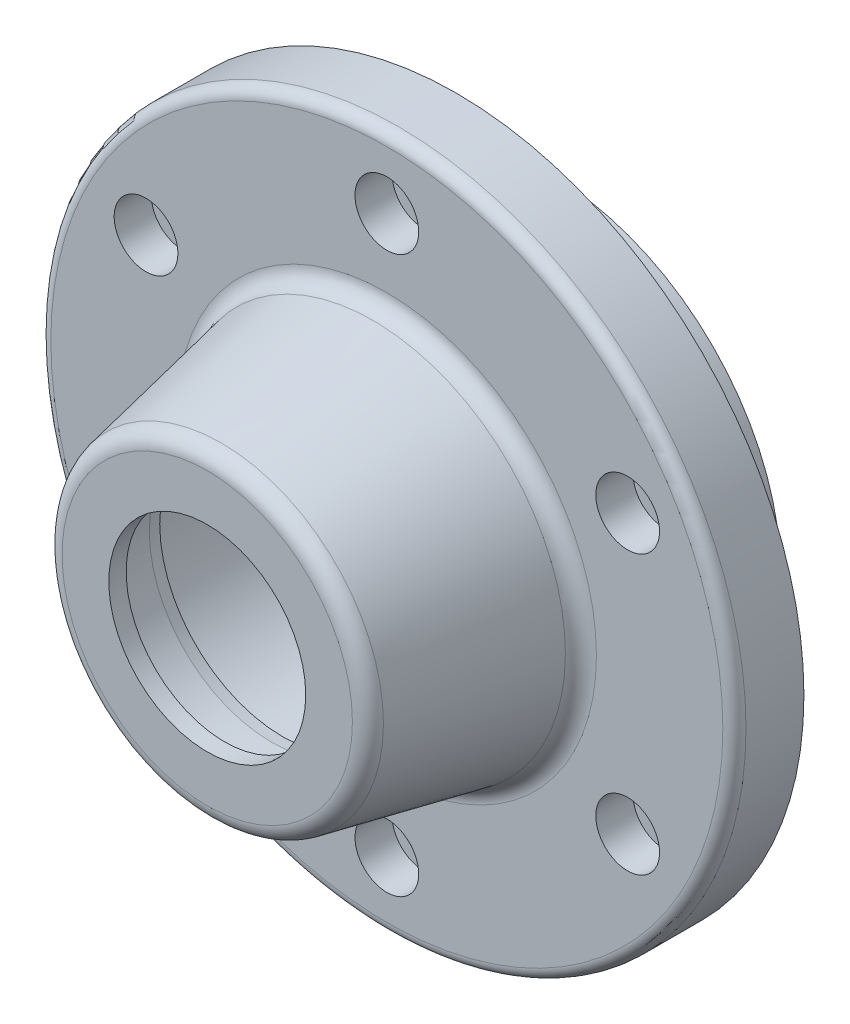
SolidWorks part; units mm, degrees
ref_plane "Front Plane" through (0, 0, 0) normal (0, 0, 1) x (1, 0, 0)
ref_plane "Top Plane" through (0, 0, 0) normal (0, 1, 0) x (1, 0, 0)
ref_plane "Right Plane" through (0, 0, 0) normal (1, 0, 0) x (0, 0, -1)
sketch "Sketch1" plane through (0, 0, 0) normal (1, 0, 0) x (0, 0, -1)
  line L0 (-82.7476, 0) -> (82.7476, 0) construction
  line L1 (55, 0) -> (-55, 0) construction
  line L2 (-63, -17) -> (-63, -25.0583)
  line L3 (-60.5883, -28) -> (-34.4117, -33.2353)
  line L4 (-32, -36.1771) -> (-32, -58)
  line L5 (-30, -60) -> (-20, -60)
  line L6 (-20, -60) -> (-20, -40)
  line L7 (-20, -40) -> (-4, -40)
  line L8 (-4, -40) -> (-4, -31)
  line L9 (-4, -31) -> (0, -31)
  line L10 (0, 55) -> (0, -55) construction
  line L11 (0, -31) -> (0, -23.75)
  line L12 (0, -23.75) -> (-3.5, -23.75)
  line L13 (-3.5, -23.75) -> (-3.5, -24.75)
  line L14 (-3.5, -24.75) -> (-5.35, -24.75)
  line L15 (-5.35, -24.75) -> (-5.35, -23.5)
  line L16 (-5.35, -23.5) -> (-21.5, -23.5)
  line L17 (-23.5, -25.5) -> (-32, -25.5)
  line L18 (-34, -23.5) -> (-50, -23.5)
  line L19 (-50, -23.5) -> (-50, -21.2102)
  line L21 (-60, -21) -> (-60, -17)
  line L22 (-60, -17) -> (-63, -17)
  line L23 (-60, -21) -> (-52, -21)
  line L24 (-52, -21) -> (-50, -21.2102)
  arc A0 (-21.5, -23.5) -> (-23.5, -25.5) centre (-23.5, -23.5) cw
  arc A1 (-32, -25.5) -> (-34, -23.5) centre (-32, -23.5) cw
  arc A2 (-32, -58) -> (-30, -60) centre (-30, -58) ccw
  arc A3 (-34.4117, -33.2353) -> (-32, -36.1771) centre (-35, -36.1771) cw
  arc A4 (-63, -25.0583) -> (-60.5883, -28) centre (-60, -25.0583) ccw
  point P29 (0, 0)
  point P33 (-54.214, -12.7252)
  point P34 (-59.6454, -11.0323)
  point P35 (-54.7078, -12.302)
  point P42 (-73.3004, -24.1523)
  point P43 (-36.7913, -38.1892)
  point P44 (-25.0115, -20.4843)
  point P45 (-22.9659, -26.6916)
  point P46 (-74.2466, -26.5506)
  point P47 (-35, -36.0908)
  point P48 (-32, -41.857)
  point P49 (-32, -48.3158)
  point P50 (0, 0)
  point P51 (-7.389, -24.75)
  dimension "D1" = 2
  dimension "D2" = 3
  dimension "D3" = 47.5
  dimension "D4" = 49.5
  dimension "D5" = 62
  dimension "D6" = 80
  dimension "D7" = 120
  dimension "D8" = 34
  dimension "D9" = 42
  dimension "D10" = 47
  dimension "D11" = 51
  dimension "D12" = 56
  dimension "D13" = 2
  dimension "D14" = 6
  dimension "D15" = 12.5
  dimension "D16" = 21.5
  dimension "D17" = 3.5
  dimension "D18" = 4
  dimension "D19" = 20
  dimension "D20" = 12
  dimension "D21" = 50
  dimension "D22" = 60
  dimension "D23" = 101.31
  dimension "D24" = 63
  dimension "D25" = 1.85
revolve "Revolve1" add sketch "Sketch1" angle 360 about L0
hole_wizard "Hole1" positions "Sketch2" profile "Sketch3" legacy end condition up to next
sketch "Sketch2" plane through (0, 0, 32) normal (0, 0, 1) x (1, 0, 0)
  line L0 (0, -34.65) -> (0, 34.65) construction
  point P0 (0, 48)
  dimension "D1" = 48
sketch "Sketch3" plane through (0, 48, 32) normal (1, 0, 0) x (0, -1, 0)
  line L0 (0, 0) -> (0, 12)
  line L1 (0, 12) -> (3.5, 12)
  line L2 (3.5, 12) -> (3.5, 6.4)
  line L3 (3.5, 6.4) -> (5.5, 6.4)
  line L4 (5.5, 6.4) -> (5.5, 0)
  line L5 (5.5, 0) -> (0, 0)
  line L6 (0, 110) -> (0, -10) construction
  dimension "Diameter" = 7
  dimension "Depth" = 12
  dimension "C-Bore Diameter" = 11
  dimension "C-Bore Depth" = 6.4
pattern_circular "CirPattern1" count 6 over 360 about axis through (0, 0, 0) along (0, 0, 1) of "Hole1"
